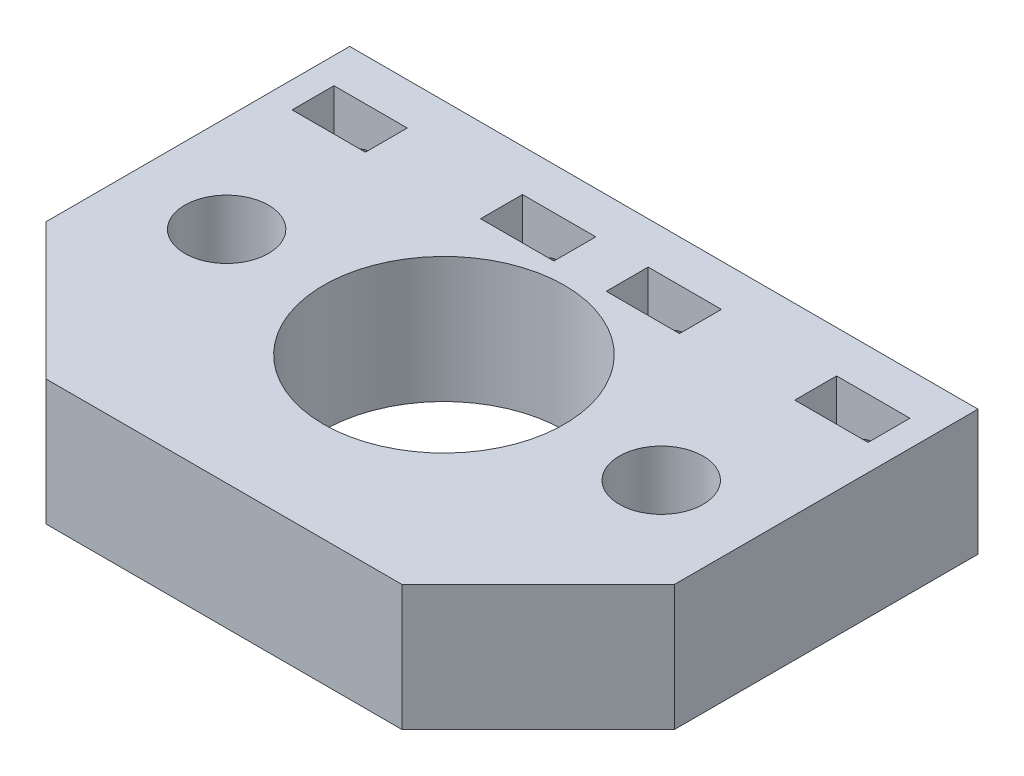
SolidWorks part; units mm, degrees
ref_plane "Front Plane" through (0, 0, 0) normal (0, 0, 1) x (1, 0, 0)
ref_plane "Top Plane" through (0, 0, 0) normal (0, 1, 0) x (1, 0, 0)
ref_plane "Right Plane" through (0, 0, 0) normal (1, 0, 0) x (0, 0, -1)
sketch "Sketch1" plane through (0, 0, 0) normal (0, 1, 0) x (1, 0, 0)
  line L1 (-30, -21) -> (30, -21)
  line L2 (-30, -21) -> (-30, 21)
  line L3 (-30, 21) -> (30, 21)
  line L4 (30, -21) -> (30, 21)
  line L5 (-30, -21) -> (30, 21) construction
  line L6 (-30, 21) -> (30, -21) construction
  point P0 (0, 0)
  dimension "D1" = 60
  dimension "D2" = 42
extrude "Boss-Extrude1" add sketch "Sketch1" along normal blind 12
sketch "Sketch3" plane through (0, 12, 0) normal (0, 1, 0) x (1, 0, 0)
  line L0 (0, 21) -> (0, -21) construction
  line L1 (30, 21) -> (-30, 21) construction
  line L2 (-30, -21) -> (30, -21) construction
  line L3 (0, 0) -> (30, 0) construction
  line L4 (30, -21) -> (30, 21) construction
  circle A0 centre (0, 0) radius 11.5
  circle A1 centre (20.75, 0) radius 4
  circle A2 centre (-20.75, 0) radius 4
  dimension "D1" = 23
  dimension "D2" = 20.75
  dimension "D3" = 8
extrude "Cut-Extrude2" cut sketch "Sketch3" against normal up to next and the other way through all
chamfer "Chamfer1" distance 13 angle 45 2 edges at (30, 6, 21) (-30, 6, 21)
sketch "Sketch5" plane through (0, 12, 0) normal (0, 1, 0) x (1, 0, 0)
  line L0 (30, 15) -> (-30, 15) construction
  line L1 (30, -8) -> (30, 21) construction
  line L2 (-30, 21) -> (-30, -8) construction
  line L3 (30, 21) -> (-30, 21) construction
  line L4 (27.5, 17) -> (20.5, 17)
  line L5 (27.5, 17) -> (27.5, 13)
  line L6 (27.5, 13) -> (20.5, 13)
  line L7 (20.5, 17) -> (20.5, 13)
  line L8 (27.5, 17) -> (20.5, 13) construction
  line L9 (27.5, 13) -> (20.5, 17) construction
  line L10 (9.5, 17) -> (9.5, 13)
  line L11 (9.5, 17) -> (2.5, 17)
  line L12 (2.5, 17) -> (2.5, 13)
  line L13 (9.5, 13) -> (2.5, 13)
  line L14 (0, 21) -> (0, 0) construction
  line L15 (-9.5, 17) -> (-2.5, 17)
  line L16 (-2.5, 17) -> (-2.5, 13)
  line L17 (-9.5, 13) -> (-2.5, 13)
  line L18 (-9.5, 17) -> (-9.5, 13)
  line L19 (-27.5, 13) -> (-20.5, 13)
  line L20 (-20.5, 17) -> (-20.5, 13)
  line L21 (-27.5, 17) -> (-20.5, 17)
  line L22 (-27.5, 17) -> (-27.5, 13)
  point P6 (24, 15)
  dimension "D1" = 7
  dimension "D2" = 4
  dimension "D3" = 6
  dimension "D4" = 6
  dimension "D6" = 18
  dimension "D5" = 2
extrude "Cut-Extrude4" cut sketch "Sketch5" against normal up to next and the other way through all
sketch "Sketch4" plane through (0, 0, -21) normal (0, 0, -1) x (-1, 0, 0)
  line L0 (-30, 6) -> (30, 6) construction
  line L1 (-30, 12) -> (-30, 0) construction
  line L2 (30, 12) -> (30, 0) construction
  line L4 (0, 0) -> (0, 12) construction
  line L5 (-30, 12) -> (30, 12) construction
  circle A0 centre (-24, 6) radius 2.25
  circle A1 centre (-6, 6) radius 2.25
  circle A2 centre (6, 6) radius 2.25
  circle A3 centre (24, 6) radius 2.25
  dimension "D1" = 4.5
  dimension "D2" = 6
  dimension "D4" = 18
  dimension "D3" = 2
extrude "Cut-Extrude3" cut sketch "Sketch4" against normal blind 7.5
